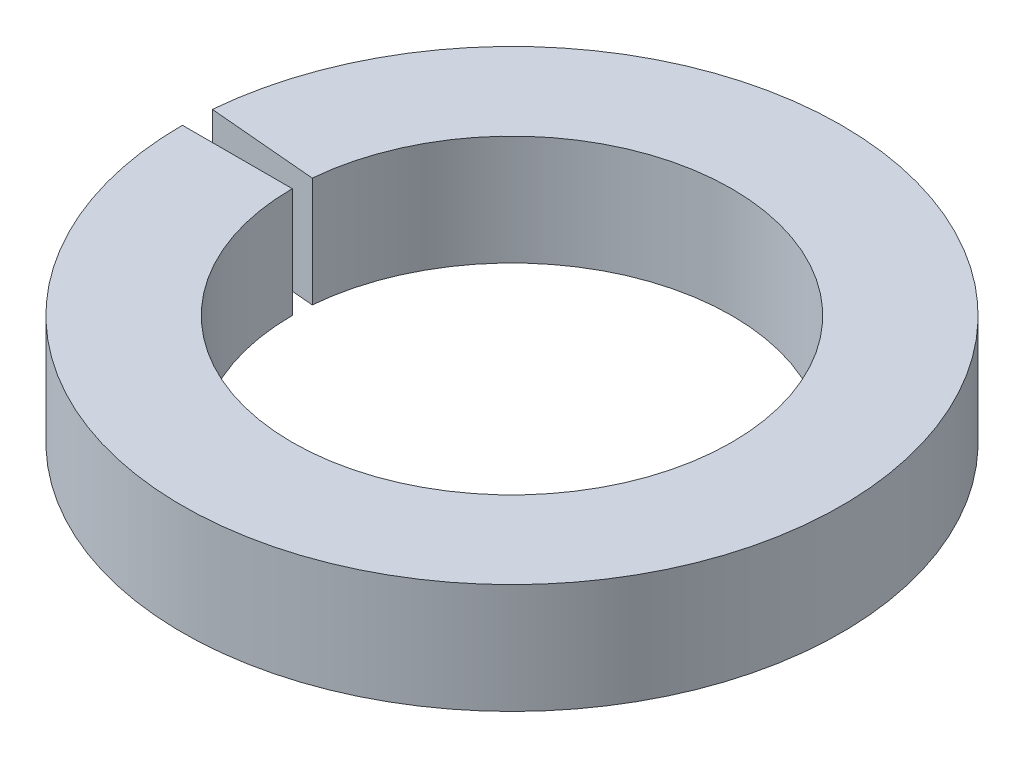
SolidWorks part; units mm, degrees
material "Zoltek Panex 33"
ref_plane "Front Plane" through (0, 0, 0) normal (0, 0, 1) x (1, 0, 0)
ref_plane "Top Plane" through (0, 0, 0) normal (0, 1, 0) x (1, 0, 0)
ref_plane "Right Plane" through (0, 0, 0) normal (1, 0, 0) x (0, 0, -1)
sketch "Sketch1" plane through (0, 0, 0) normal (0, 0, 1) x (1, 0, 0)
  line L0 (0, 0) -> (0, 3.175) construction
  line L2 (-9.525, 0) -> (-6.35, 0)
  line L3 (-9.525, 0) -> (-9.525, 3.175)
  line L4 (-9.525, 3.175) -> (-6.35, 3.175)
  line L5 (-6.35, 0) -> (-6.35, 3.175)
  dimension "D1" = 3.175
  dimension "D2" = 12.7
  dimension "D3" = 3.175
revolve "Revolve1" add sketch "Sketch1" angle 355 about L0
